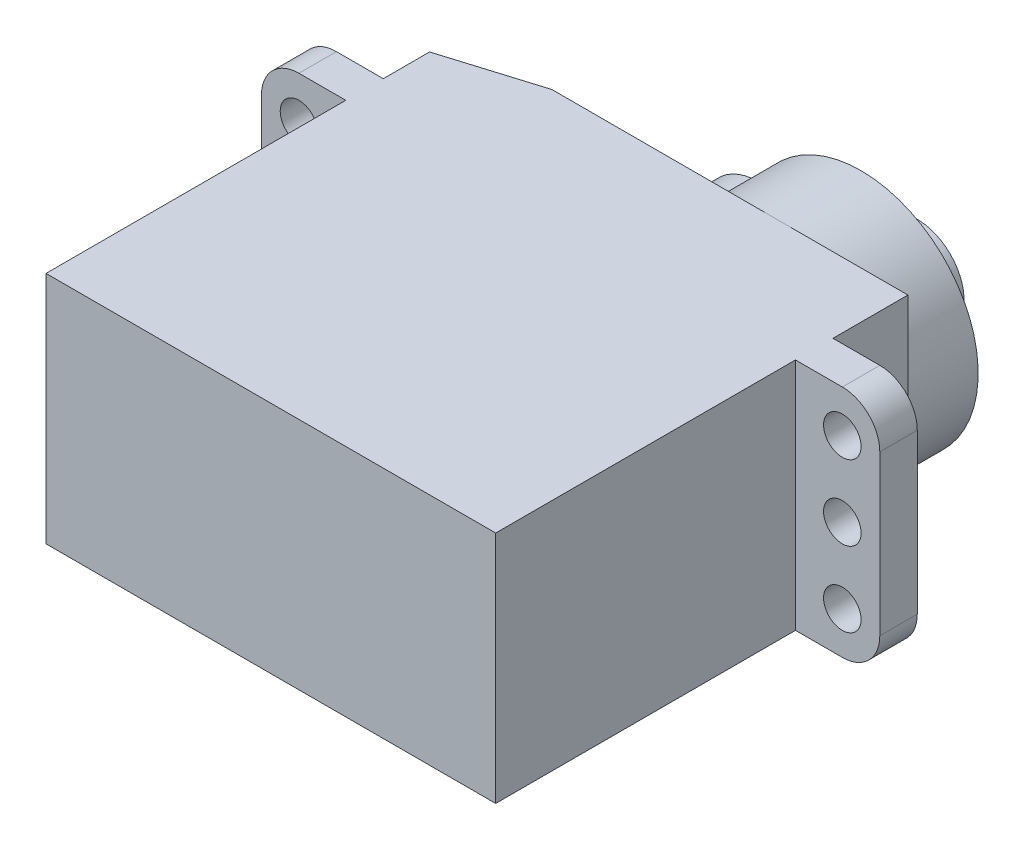
SolidWorks part; units mm, degrees
ref_plane "Front Plane" through (0, 0, 0) normal (0, 0, 1) x (1, 0, 0)
ref_plane "Top Plane" through (0, 0, 0) normal (0, 1, 0) x (1, 0, 0)
ref_plane "Right Plane" through (0, 0, 0) normal (1, 0, 0) x (0, 0, -1)
sketch "Sketch1" plane through (0, 0, 0) normal (0, 1, 0) x (1, 0, 0)
  line L0 (-12, 0) -> (-12, 16)
  line L1 (-12, 16) -> (-16.5, 16)
  line L2 (-16.5, 16) -> (-16.5, 18)
  line L3 (-16.5, 18) -> (-12, 18)
  line L4 (-12, 18) -> (-12, 22)
  line L5 (-12, 22) -> (12, 22)
  line L6 (12, 22) -> (12, 18)
  line L7 (12, 18) -> (16.5, 18)
  line L8 (16.5, 18) -> (16.5, 16)
  line L9 (16.5, 16) -> (12, 16)
  line L10 (12, 16) -> (12, 0)
  line L11 (12, 0) -> (-12, 0)
  point P3 (0, 0)
  point P14 (0, 0)
  point P15 (0, 0)
  point P16 (0, 0)
  point P17 (0, 0)
  dimension "D1" = 4.5
  dimension "D2" = 4.5
  dimension "D3" = 2
  dimension "D4" = 4
  dimension "D5" = 24
  dimension "D6" = 22
extrude "Boss-Extrude1" add sketch "Sketch1" along normal blind 12.5
sketch "Sketch2" plane through (0, 0, -22) normal (0, 0, -1) x (-1, 0, 0)
  line L0 (-12, 6.25) -> (12, 6.25) construction
  line L1 (-12, 12.5) -> (-12, 0) construction
  line L2 (12, 12.5) -> (12, 0) construction
  line L3 (-12, 12.5) -> (12, 12.5) construction
  line L5 (0.4829, 9.25) -> (0.4829, 3.25) construction
  circle A0 centre (-5, 6.25) radius 6.25
  circle A1 centre (0.4829, 6.25) radius 3
  point P14 (-13.1877, 6.25)
  point P15 (0, 0)
  dimension "D1" = 7
  dimension "D2" = 6
extrude "Boss-Extrude2" add sketch "Sketch2" along normal blind 4.5 contours A1 A0 | A0 A1 | A0 A1
sketch "Sketch3" plane through (0, 0, -26.5) normal (0, 0, -1) x (-1, 0, 0)
  line L0 (-5, 0) -> (-5, 12.5) construction
  arc A0 (0.4829, 9.25) -> (0.4829, 3.25) centre (-5, 6.25) ccw construction
  circle A1 centre (-5, 6.25) radius 2.5
  circle A2 centre (-5, 6.25) radius 1
  dimension "D1" = 2
  dimension "D2" = 5
extrude "Boss-Extrude3" add sketch "Sketch3" along normal blind 3
sketch "Sketch4" plane through (0, 0, -18) normal (0, 0, -1) x (-1, 0, 0)
  line L0 (-14.5, 12.5) -> (-14.5, 0) construction
  line L1 (-16.5, 12.5) -> (-12, 12.5) construction
  line L2 (-16.5, 0) -> (-12, 0) construction
  line L3 (-16.5, 12.5) -> (-16.5, 0) construction
  circle A0 centre (-14.5, 6.25) radius 1
  circle A1 centre (-14.5, 10.25) radius 1
  circle A2 centre (-14.5, 2.25) radius 1
  dimension "D1" = 2
  dimension "D2" = 2
  dimension "D4" = 2
  dimension "D3" = 2
extrude "Cut-Extrude1" cut sketch "Sketch4" against normal up to next (2 mm away)
mirror "Mirror1" about plane through (0, 0, 0) normal (1, 0, 0) of "Cut-Extrude1"
fillet "Fillet1" radius 2 4 edges at (-16.5, 0, -17) (-16.5, 12.5, -17) (16.5, 0, -17) (16.5, 12.5, -17)
chamfer "Chamfer1" distance 5 angle 17 1 edges at (-12, 6.25, -22)
